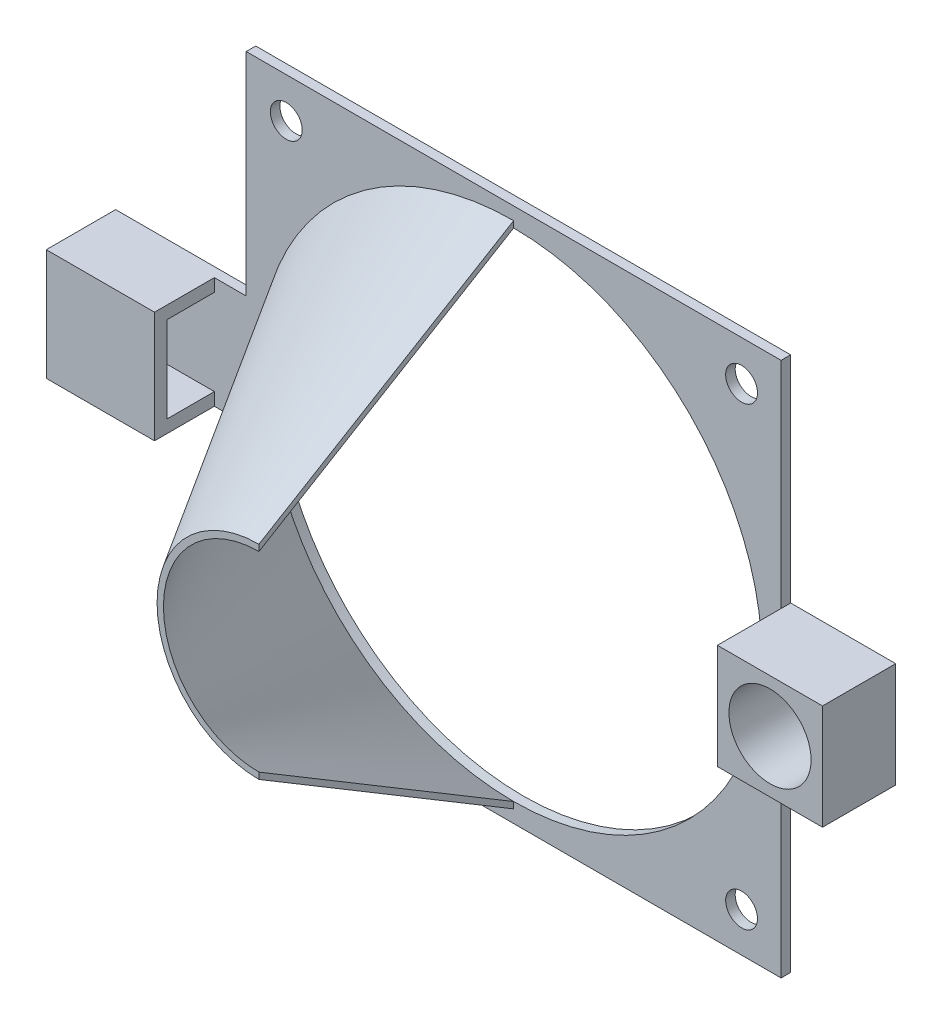
SolidWorks part; units mm, degrees
ref_plane "Alzado" through (0, 0, 0) normal (0, 0, 1) x (1, 0, 0)
ref_plane "Planta" through (0, 0, 0) normal (0, 1, 0) x (1, 0, 0)
ref_plane "Vista lateral" through (0, 0, 0) normal (1, 0, 0) x (0, 0, -1)
sketch "Croquis1" plane through (0, 0, 0) normal (0, 0, 1) x (1, 0, 0)
  line L0 (-103.3198, -49.5061) -> (-19.3198, 34.4939) construction
  line L1 (-103.3198, 34.4939) -> (-19.3198, 34.4939)
  line L2 (-103.3198, 34.4939) -> (-103.3198, -49.5061)
  line L3 (-103.3198, -49.5061) -> (-19.3198, -49.5061)
  line L4 (-19.3198, 34.4939) -> (-19.3198, -49.5061)
  line L5 (-19.3198, -49.5061) -> (-103.3198, 34.4939) construction
  circle A0 centre (-61.3198, -7.5061) radius 39
  circle A1 centre (-97.0287, 28.2028) radius 2.5
  circle A2 centre (-25.5287, 28.2028) radius 2.5
  circle A3 centre (-25.5287, -43.2972) radius 2.5
  circle A4 centre (-97.0287, -43.2972) radius 2.5
  dimension "D3" = 50.5
  dimension "D4" = 2
  dimension "D1" = 84
  dimension "D2" = 84
  dimension "D5" = 2
extrude "Saliente-Extruir1" add sketch "Croquis1" along normal blind 1.5
ref_plane "Plano1" through (-61.3198, -49.5061, 1.5) normal (1, 0, 0) x (0, 0, -1)
sketch "Croquis4" plane through (-61.3198, -49.5061, 1.5) normal (1, 0, 0) x (0, 0, -1)
  line L0 (0, 3) -> (0, 42) construction
  line L1 (0, 42) -> (-40, 42) construction
  line L2 (-40, 42) -> (-40, 27) construction
  line L3 (-40, 27) -> (0, 3)
  line L4 (0, 3) -> (0, 2)
  line L5 (0, 2) -> (-40, 26)
  line L6 (-40, 26) -> (-40, 27)
revolve "Revolución2" add sketch "Croquis4" angle 180 about L1
sketch "Croquis6" plane through (-103.3198, 0, 0) normal (-1, 0, 0) x (0, 0, 1)
  line L0 (0, -7.5061) -> (0, -16.2561)
  line L1 (0, 34.4939) -> (0, -49.5061) construction
  line L2 (0, -16.2561) -> (1.5, -16.2561)
  line L3 (1.5, 34.4939) -> (1.5, -49.5061) construction
  line L4 (1.5, -16.2561) -> (1.5, 1.2439)
  line L5 (1.5, 1.2439) -> (0, 1.2439)
  line L6 (0, 1.2439) -> (0, -7.5061)
extrude "Saliente-Extruir2" add sketch "Croquis6" along normal blind 20
sketch "Croquis7" plane through (-123.3198, 0, 0) normal (-1, 0, 0) x (0, 0, 1)
  line L0 (1.5, 1.2439) -> (1.5, -0.7561) construction
  line L1 (1.5, 1.2439) -> (10.9, 1.2439)
  line L2 (1.5, 1.2439) -> (1.5, -16.2561)
  line L3 (1.5, -16.2561) -> (10.9, -16.2561)
  line L4 (10.9, 1.2439) -> (10.9, -16.2561)
  line L5 (1.5, -16.2561) -> (1.5, -14.2561) construction
  line L7 (1.5, -0.7561) -> (8.9, -0.7561)
  line L8 (1.5, -0.7561) -> (1.5, -14.2561)
  line L9 (1.5, -14.2561) -> (8.9, -14.2561)
  line L10 (8.9, -0.7561) -> (8.9, -14.2561)
  line M6 (1.5, -16.2561) -> (1.5, 1.2439)
  dimension "D1" = 9.4
  dimension "D2" = 2
extrude "Saliente-Extruir3" add sketch "Croquis7" against normal blind 15 contours L7 L10 L9 L3 L4 L1 L2 M6
sketch "Croquis8" plane through (-123.3198, 0, 0) normal (-1, 0, 0) x (0, 0, 1)
  line L0 (10.9, -16.2561) -> (0, 1.2439) construction
  line L1 (0, 1.2439) -> (10.9, 1.2439)
  line L2 (0, 1.2439) -> (0, -16.2561)
  line L3 (0, -16.2561) -> (10.9, -16.2561)
  line L4 (10.9, 1.2439) -> (10.9, -16.2561)
  line L5 (10.9, 1.2439) -> (0, -16.2561) construction
  circle A0 centre (5.45, -7.5061) radius 3.6
extrude "Saliente-Extruir4" add sketch "Croquis8" along normal blind 2
sketch "Croquis9" plane through (-19.3198, 0, 0) normal (1, 0, 0) x (0, 0, -1)
  line L0 (0, -7.5061) -> (0, 0.7439)
  line L1 (0, -49.5061) -> (0, 34.4939) construction
  line L2 (0, 0.7439) -> (-1.5, 0.7439)
  line L3 (-1.5, -49.5061) -> (-1.5, 34.4939) construction
  line L4 (-1.5, 0.7439) -> (-1.5, -15.7561)
  line L5 (-1.5, -15.7561) -> (0, -15.7561)
  line L6 (0, -15.7561) -> (0, -7.5061)
extrude "Saliente-Extruir5" add sketch "Croquis9" along normal blind 16.5
sketch "Croquis10" plane through (0, 0, 1.5) normal (0, 0, 1) x (1, 0, 0)
  line L0 (-2.8198, -15.7561) -> (-19.3198, 0.7439) construction
  line L1 (-19.3198, -15.7561) -> (-2.8198, -15.7561)
  line L2 (-19.3198, -15.7561) -> (-19.3198, 0.7439)
  line L3 (-19.3198, 0.7439) -> (-2.8198, 0.7439)
  line L4 (-2.8198, -15.7561) -> (-2.8198, 0.7439)
  line L5 (-2.8198, 0.7439) -> (-19.3198, -15.7561) construction
  circle A0 centre (-11.0698, -7.5061) radius 6.45
extrude "Saliente-Extruir6" add sketch "Croquis10" along normal blind 10
